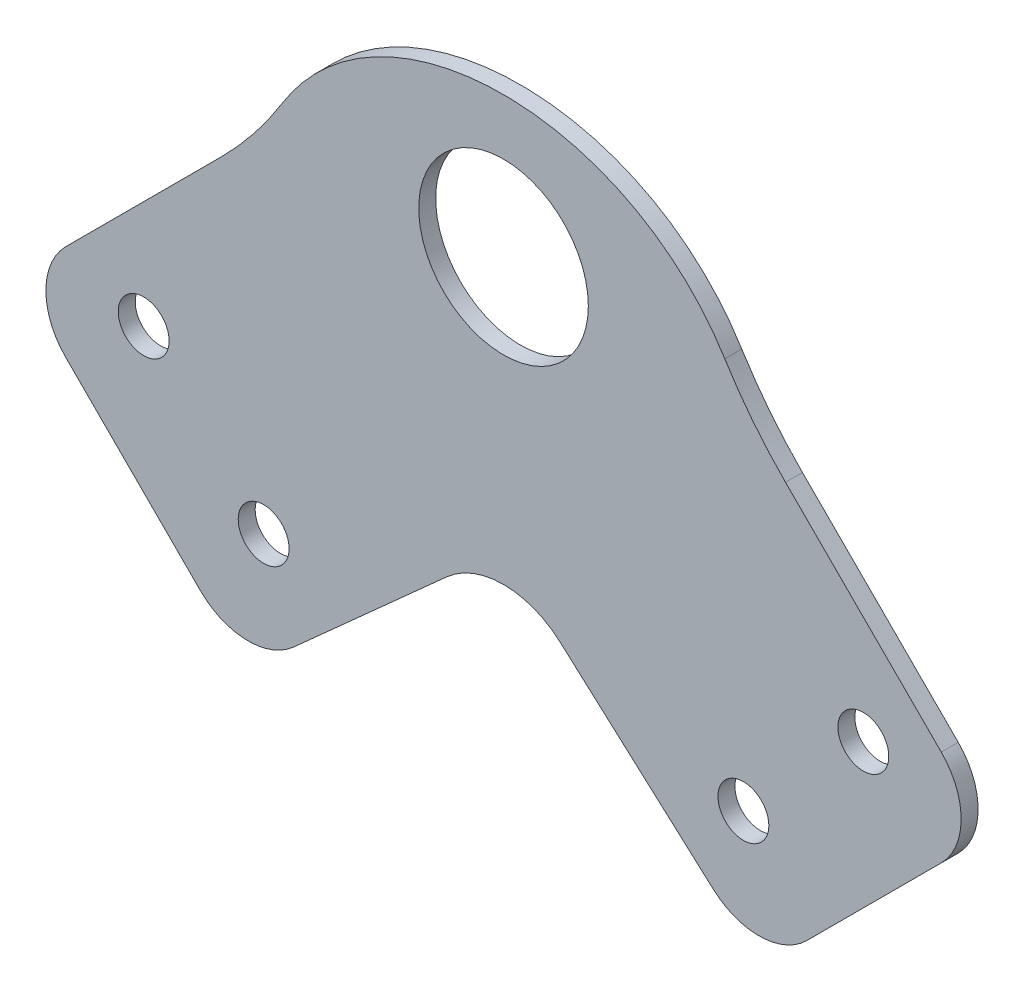
SolidWorks part; units mm, degrees
ref_plane "Front Plane" through (0, 0, 0) normal (0, 0, 1) x (1, 0, 0)
ref_plane "Top Plane" through (0, 0, 0) normal (0, 1, 0) x (1, 0, 0)
ref_plane "Right Plane" through (0, 0, 0) normal (1, 0, 0) x (0, 0, -1)
sketch "Sketch1" plane through (0, 0, 0) normal (0, 0, 1) x (1, 0, 0)
  line L0 (5.8771, 5.8771) -> (-44.5049, -44.5049) construction
  line L1 (0, -69.3528) -> (0, 69.3528) construction
  line L2 (0, 0) -> (64.8331, -64.8331) construction
  line L3 (-57.2756, -30.4056) -> (-28.1258, -1.2558)
  line L4 (57.2756, -30.4056) -> (28.1258, -1.2558)
  line L5 (-57.2756, -30.4056) -> (-30.4056, -57.2756)
  line L6 (-30.4056, -57.2756) -> (0, -30)
  line L7 (57.2756, -30.4056) -> (30.4056, -57.2756)
  line L8 (30.4056, -57.2756) -> (0, -30)
  circle A0 centre (0, 0) radius 10
  circle A1 centre (-42.4264, -28.2843) radius 3
  circle A2 centre (-28.2843, -42.4264) radius 3
  circle A3 centre (28.2843, -42.4264) radius 3
  circle A4 centre (42.4264, -28.2843) radius 3
  spline S0 degree 3 poles (-28.1258, -1.2558) (-17.9043, 22.5439) (17.9043, 22.5439) (28.1258, -1.2558) knots 0 0 0 0 1 1 1 1
  point P0 (0, 0)
  point P21 (-43.8406, -43.8406)
  dimension "D3" = 20
  dimension "D4" = 6
  dimension "D5" = 10
  dimension "D1" = 45
  dimension "D2" = 45
  dimension "D6" = 50
  dimension "D7" = 38
  dimension "D8" = 30
  dimension "D9" = 12
extrude "Boss-Extrude1" add sketch "Sketch1" along normal blind 2
fillet "Fillet1" radius 10 1 edges at (0, -30, 1)
fillet "Fillet2" radius 8 4 edges at (57.2756, -30.4056, 1) (30.4056, -57.2756, 1) (-57.2756, -30.4056, 1) (-30.4056, -57.2756, 1)
fillet "Fillet3" radius 50 2 edges at (-28.1258, -1.2558, 1) (28.1258, -1.2558, 1)
sketch "Sketch2" plane through (0, 0, 2) normal (0, 0, 1) x (1, 0, 0)
  line L1 (-3.5, -3.5) -> (3.5, -3.5)
  line L2 (-3.5, -3.5) -> (-3.5, 3.5)
  line L3 (-3.5, 3.5) -> (3.5, 3.5)
  line L4 (3.5, -3.5) -> (3.5, 3.5)
  line L5 (-3.5, -3.5) -> (3.5, 3.5) construction
  line L6 (-3.5, 3.5) -> (3.5, -3.5) construction
  point P0 (0, 0)
  dimension "D1" = 7
  dimension "D2" = 7
extrude "Cut-Extrude1" [suppressed] cut sketch "Sketch2" against normal through all
